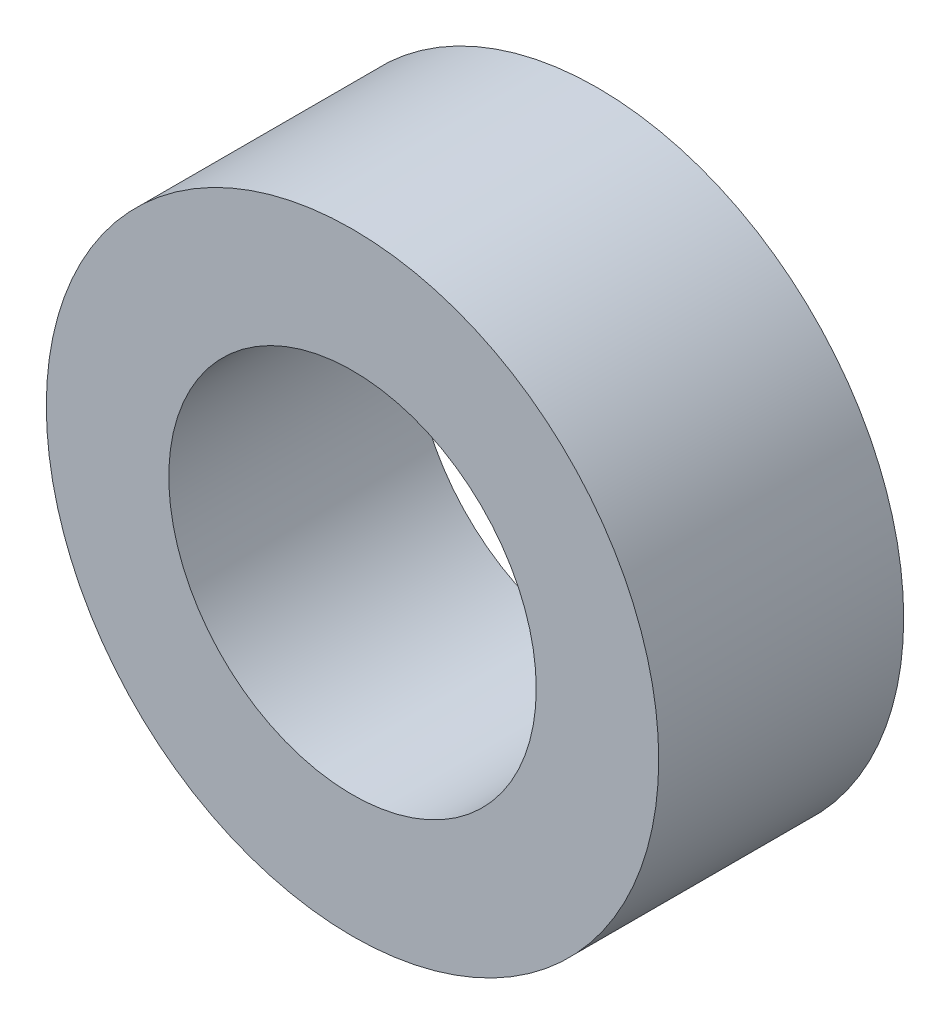
SolidWorks part; units mm, degrees
ref_plane "Спереди" through (0, 0, 0) normal (0, 0, 1) x (1, 0, 0)
ref_plane "Сверху" through (0, 0, 0) normal (0, 1, 0) x (1, 0, 0)
ref_plane "Справа" through (0, 0, 0) normal (1, 0, 0) x (0, 0, -1)
sketch "Эскиз1" plane through (0, 0, 0) normal (0, 0, 1) x (1, 0, 0)
  circle A0 centre (0, 0) radius 1.5
  circle A1 centre (0, 0) radius 2.5
  dimension "D1" = 3
  dimension "D2" = 5
extrude "Бобышка-Вытянуть1" add sketch "Эскиз1" along normal blind 2
